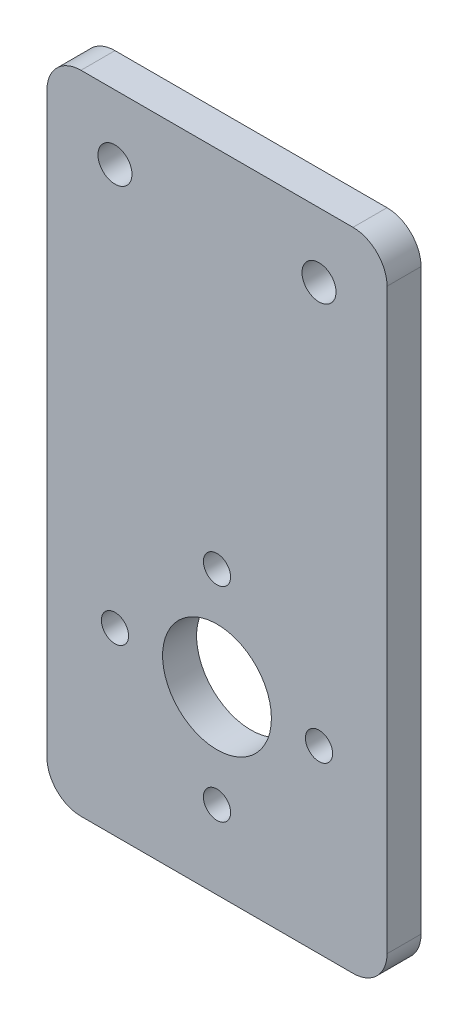
SolidWorks part; units mm, degrees
material "6061 Alloy"
ref_plane "Front Plane" through (0, 0, 0) normal (0, 0, 1) x (1, 0, 0)
ref_plane "Top Plane" through (0, 0, 0) normal (0, 1, 0) x (1, 0, 0)
ref_plane "Right Plane" through (0, 0, 0) normal (1, 0, 0) x (0, 0, -1)
sketch "Sketch1" plane through (0, 0, 0) normal (0, 0, 1) x (1, 0, 0)
  line L1 (0, 0) -> (50, 0)
  line L2 (0, 0) -> (0, -95)
  line L3 (0, -95) -> (50, -95)
  line L4 (50, 0) -> (50, -95)
  circle A0 centre (10, -9.5) radius 2.5
  circle A1 centre (40, -9.5) radius 2.5
  circle A2 centre (25, -68.525) radius 8
  circle A3 centre (25, -68.525) radius 15 construction
  circle A4 centre (25, -53.525) radius 2
  circle A5 centre (40, -68.525) radius 2
  circle A6 centre (25, -83.525) radius 2
  circle A7 centre (10, -68.525) radius 2
  point P14 (0, 0)
  point P23 (25, -68.525)
  dimension "D3" = 5
  dimension "D6" = 30
  dimension "D9" = 30
  dimension "D10" = 16
  dimension "D11" = 4
  dimension "D1" = 50
  dimension "D2" = 95
  dimension "D4" = 9.5
  dimension "D5" = 10
  dimension "D7" = 68.525
  dimension "D8" = 25
  dimension "D12" = 4
extrude "Boss-Extrude1" add sketch "Sketch1" along normal blind 5
fillet "Fillet1" radius 5 4 edges at (50, -95, 2.5) (0, -95, 2.5) (0, 0, 2.5) (50, 0, 2.5)
